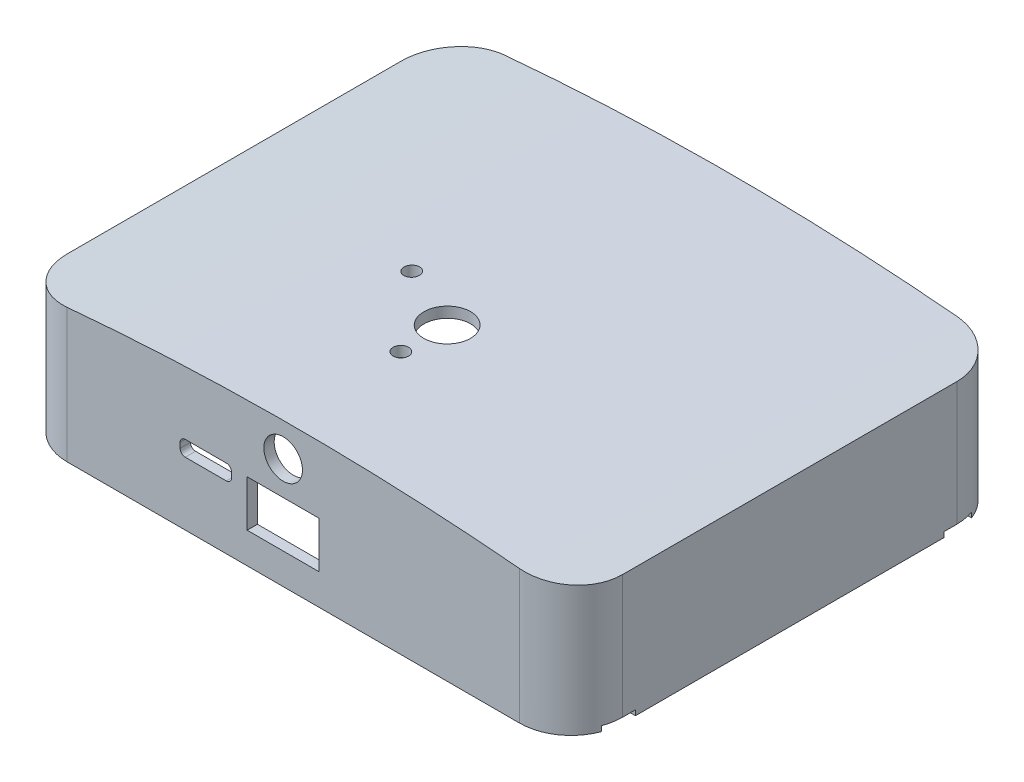
SolidWorks part; units mm, degrees
ref_plane "Front Plane" through (0, 0, 0) normal (0, 0, 1) x (1, 0, 0)
ref_plane "Top Plane" through (0, 0, 0) normal (0, 1, 0) x (1, 0, 0)
ref_plane "Right Plane" through (0, 0, 0) normal (1, 0, 0) x (0, 0, -1)
ref_plane "Plane2" through (0, 0, -85) normal (0, 0, 1) x (1, 0, 0)
ref_plane "Plane3" through (0, 2, 0) normal (0, 1, 0) x (1, 0, 0)
sketch "Sketch10" plane through (0, 2, 0) normal (0, 1, 0) x (1, 0, 0)
  line L0 (57.999, 83) -> (-30.001, 83)
  line L1 (-38.001, 75) -> (-38.001, 10)
  line L2 (-30.001, 2) -> (57.999, 2)
  line L3 (65.999, 10) -> (65.999, 75)
  line L12 (67.999, 10) -> (67.999, 75)
  line L13 (-30.001, 0) -> (57.999, 0)
  line L14 (-40.001, 75) -> (-40.001, 10)
  line L15 (57.999, 85) -> (-30.001, 85)
  arc A0 (65.999, 75) -> (57.999, 83) centre (57.999, 75) ccw
  arc A1 (-30.001, 83) -> (-38.001, 75) centre (-30.001, 75) ccw
  arc A2 (-38.001, 10) -> (-30.001, 2) centre (-30.001, 10) ccw
  arc A3 (57.999, 2) -> (65.999, 10) centre (57.999, 10) ccw
  arc A12 (67.999, 75) -> (57.999, 85) centre (57.999, 75) ccw
  arc A13 (57.999, 0) -> (67.999, 10) centre (57.999, 10) ccw
  arc A14 (-40.001, 10) -> (-30.001, 0) centre (-30.001, 10) ccw
  arc A15 (-30.001, 85) -> (-40.001, 75) centre (-30.001, 75) ccw
  dimension "D1" = 2
extrude "Boss-Extrude5" add sketch "Sketch10" along normal blind 42
sketch "Sketch20" plane through (0, 0, 0) normal (0, 0, 1) x (1, 0, 0)
  line L0 (-40.001, 25) -> (67.999, 25) construction
  line L1 (-32.001, 5) -> (18.999, 5) construction
  line L2 (-32.001, 5) -> (-32.001, 25) construction
  line L3 (-32.001, 25) -> (18.999, 25) construction
  line L4 (18.999, 5) -> (18.999, 25) construction
  line L5 (-40.001, 44) -> (-40.001, 2) construction
  line L6 (67.999, 44) -> (67.999, 2) construction
  line L7 (13.999, 25) -> (13.999, 27.03) construction
  line L9 (13.999, 25) -> (13.999, 28.9912) construction
  line L10 (13.999, 25) -> (13.999, 30.9628) construction
  line L11 (-40.001, 25) -> (-40.001, 27.03)
  line L12 (67.999, 25) -> (67.999, 27.03)
  line L13 (13.999, 25) -> (13.999, 27.9584) construction
  line L14 (13.999, 25) -> (13.999, 30.0146) construction
  spline S1 degree 2 poles (-40.001, 25) (13.999, 30.9168) (67.999, 25) knots 0 0 0 1 1 1
  spline S2 degree 2 poles (67.999, 27.03) (13.999, 32.9992) (-40.001, 27.03) knots 0 0 0 1 1 1
  dimension "D1" = 20
sketch "Sketch22" plane through (0, 0, 0) normal (0, 0, 1) x (1, 0, 0)
  line L0 (67.999, 44) -> (67.999, 2) construction
  line L1 (67.999, 44) -> (57.999, 44) construction
  line L2 (-30.001, 44) -> (-40.001, 44) construction
  line L3 (-30.001, 44) -> (57.999, 44) construction
  line L4 (-40.001, 44) -> (-40.001, 2) construction
  line L5 (67.999, 44) -> (67.999, 25)
  line L6 (67.999, 44) -> (57.999, 44)
  line L7 (-30.001, 44) -> (-40.001, 44)
  line L8 (-30.001, 44) -> (57.999, 44)
  line L9 (-40.001, 44) -> (-40.001, 25)
  line L10 (-40.001, 25) -> (67.999, 25) construction
  line L11 (13.999, 25) -> (13.999, 28.0496) construction
  spline S0 degree 2 poles (-40.001, 25) (13.999, 31.0992) (67.999, 25) knots 0 0 0 1 1 1
extrude "Cut-Extrude6" cut sketch "Sketch22" against normal blind 95
extrude "Boss-Extrude8" add sketch "Sketch20" against normal blind 85
sketch "Sketch23" plane through (0, 2, 0) normal (0, -1, 0) x (1, 0, 0)
  line L0 (-40.001, -75) -> (-40.001, -85) construction
  line L1 (-40.001, -85) -> (-30.001, -85) construction
  line L2 (57.999, -85) -> (67.999, -85) construction
  line L3 (67.999, -85) -> (67.999, -75) construction
  line L4 (67.999, -10) -> (67.999, 0) construction
  line L5 (67.999, 0) -> (57.999, 0) construction
  line L6 (-30.001, 0) -> (-40.001, 0) construction
  line L7 (-40.001, 0) -> (-40.001, -10) construction
  line L8 (-40.001, -75) -> (-40.001, -85)
  line L9 (-40.001, -85) -> (-30.001, -85)
  line L10 (57.999, -85) -> (67.999, -85)
  line L11 (67.999, -85) -> (67.999, -75)
  line L12 (67.999, -10) -> (67.999, 0)
  line L13 (67.999, 0) -> (57.999, 0)
  line L14 (-30.001, 0) -> (-40.001, 0)
  line L15 (-40.001, 0) -> (-40.001, -10)
  arc A0 (-40.001, -75) -> (-30.001, -85) centre (-30.001, -75) ccw construction
  arc A1 (57.999, -85) -> (67.999, -75) centre (57.999, -75) ccw construction
  arc A2 (67.999, -10) -> (57.999, 0) centre (57.999, -10) ccw construction
  arc A3 (-30.001, 0) -> (-40.001, -10) centre (-30.001, -10) ccw construction
  arc A4 (-40.001, -75) -> (-30.001, -85) centre (-30.001, -75) ccw
  arc A5 (57.999, -85) -> (67.999, -75) centre (57.999, -75) ccw
  arc A6 (67.999, -10) -> (57.999, 0) centre (57.999, -10) ccw
  arc A7 (-30.001, 0) -> (-40.001, -10) centre (-30.001, -10) ccw
extrude "Cut-Extrude7" cut sketch "Sketch23" against normal blind 85
sketch "Sketch26" plane through (0, 0, 0) normal (0, 0, 1) x (1, 0, 0)
  line L0 (-32.001, 5) -> (18.999, 5) construction
  line L1 (-40.001, 14.515) -> (67.999, 14.515) construction
  line L2 (-40.001, 27.03) -> (-40.001, 2) construction
  line L3 (67.999, 27.03) -> (67.999, 2) construction
  line L4 (13.999, 14.515) -> (13.999, 36.3942) construction
  line L5 (18.999, 5) -> (18.999, 26.3407) construction
  line L6 (4.999, 17) -> (18.999, 17)
  line L7 (4.999, 17) -> (4.999, 8)
  line L8 (4.999, 8) -> (18.999, 8)
  line L9 (18.999, 17) -> (18.999, 8)
  line L10 (11.999, 17) -> (11.999, 30.0105) construction
  circle A0 centre (11.999, 23.5) radius 3.75
  parabola Q0 (57.999, 28.033) -> (-30.001, 28.033) focus (13.999, -214.2381) apex (13.999, 30.0146) construction
  dimension "D6" = 7.5
  dimension "D1" = 14
  dimension "D2" = 9
  dimension "D3" = 0
  dimension "D4" = 3
  dimension "D5" = 6.5
extrude "Cut-Extrude9" cut sketch "Sketch26" against normal blind 15 contours L9 L6 L7 L8 | A0
sketch "Sketch28" plane through (0, 2, 0) normal (0, -1, 0) x (1, 0, 0)
  line L4 (-30.001, -85) -> (57.999, -85)
  line L5 (67.999, -75) -> (67.999, -10)
  line L6 (57.999, 0) -> (-30.001, 0)
  line L7 (-40.001, -10) -> (-40.001, -75)
  line L9 (67.999, -75) -> (67.999, -72.5)
  line L11 (-40.001, -10) -> (-40.001, -12.5)
  line L18 (63.999, -12.5) -> (67.999, -12.5)
  line L19 (67.3665, -6.5) -> (63.999, -6.5)
  line L20 (63.999, -78.5) -> (67.3665, -78.5)
  line L21 (-40.001, -72.5) -> (-40.001, -75)
  line L22 (67.999, -72.5) -> (63.999, -72.5)
  line L23 (-39.3685, -78.5) -> (-36.001, -78.5)
  line L24 (-36.001, -72.5) -> (-40.001, -72.5)
  line L26 (-40.001, -12.5) -> (-36.001, -12.5)
  line L27 (-36.001, -6.5) -> (-39.3685, -6.5)
  line L28 (67.999, -12.5) -> (67.999, -10)
  arc A4 (57.999, -85) -> (67.999, -75) centre (57.999, -75) ccw
  arc A5 (67.999, -10) -> (57.999, 0) centre (57.999, -10) ccw
  arc A6 (-30.001, 0) -> (-40.001, -10) centre (-30.001, -10) ccw
  arc A7 (-40.001, -75) -> (-30.001, -85) centre (-30.001, -75) ccw
  arc A8 (67.3665, -78.5) -> (67.999, -75) centre (57.999, -75) ccw
  arc A9 (67.999, -10) -> (67.3665, -6.5) centre (57.999, -10) ccw
  arc A10 (-39.3685, -6.5) -> (-40.001, -10) centre (-30.001, -10) ccw
  arc A11 (-40.001, -75) -> (-39.3685, -78.5) centre (-30.001, -75) ccw
  arc A16 (63.999, -6.5) -> (63.999, -12.5) centre (63.999, -9.5) ccw
  arc A19 (63.999, -72.5) -> (63.999, -78.5) centre (63.999, -75.5) ccw
  arc A21 (-36.001, -78.5) -> (-36.001, -72.5) centre (-36.001, -75.5) ccw
  arc A23 (-36.001, -12.5) -> (-36.001, -6.5) centre (-36.001, -9.5) ccw
  dimension "D1" = 0
extrude "Boss-Extrude9" add sketch "Sketch28" against normal blind 15
sketch "Sketch29" plane through (0, 2, 0) normal (0, -1, 0) x (1, 0, 0)
  line L14 (67.999, -72.5) -> (67.999, -75)
  line L15 (63.999, -12.5) -> (67.999, -12.5)
  line L16 (67.3665, -6.5) -> (63.999, -6.5)
  line L17 (-40.001, -12.5) -> (-40.001, -10)
  line L18 (67.999, -10) -> (67.999, -12.5)
  line L19 (67.999, -72.5) -> (63.999, -72.5)
  line L20 (63.999, -78.5) -> (67.3665, -78.5)
  line L22 (-39.3685, -78.5) -> (-36.001, -78.5)
  line L23 (-36.001, -72.5) -> (-40.001, -72.5)
  line L24 (-40.001, -75) -> (-40.001, -72.5)
  line L26 (-40.001, -12.5) -> (-36.001, -12.5)
  line L27 (-36.001, -6.5) -> (-39.3685, -6.5)
  arc A12 (67.999, -10) -> (67.3665, -6.5) centre (57.999, -10) ccw
  arc A14 (63.999, -6.5) -> (63.999, -12.5) centre (63.999, -9.5) ccw
  arc A16 (67.3665, -78.5) -> (67.999, -75) centre (57.999, -75) ccw
  arc A17 (63.999, -72.5) -> (63.999, -78.5) centre (63.999, -75.5) ccw
  arc A18 (-40.001, -75) -> (-39.3685, -78.5) centre (-30.001, -75) ccw
  arc A20 (-36.001, -78.5) -> (-36.001, -72.5) centre (-36.001, -75.5) ccw
  arc A22 (-39.3685, -6.5) -> (-40.001, -10) centre (-30.001, -10) ccw
  arc A23 (-36.001, -12.5) -> (-36.001, -6.5) centre (-36.001, -9.5) ccw
extrude "Cut-Extrude11" cut sketch "Sketch29" against normal blind 1
sketch "Sketch30" plane through (0, 3, 0) normal (0, -1, 0) x (1, 0, 0)
  circle A0 centre (-36.001, -9.5) radius 1.4
  circle A1 centre (63.999, -9.5) radius 1.4
  circle A2 centre (63.999, -75.5) radius 1.4
  circle A3 centre (-36.001, -75.5) radius 1.4
extrude "Cut-Extrude12" cut sketch "Sketch30" against normal blind 15
sketch "Sketch31" plane through (-40.001, 0, 0) normal (-1, 0, 0) x (0, 0, 1)
  line L0 (-58.5, 8.5) -> (-58.5, 20.9923) construction
  line L1 (-72.5, 2) -> (-12.5, 2) construction
  line L3 (-62.5639, 14.4802) -> (-54.6165, 14.4802) construction
  line L4 (-63.5, 8.5) -> (-53.5, 8.5)
  line L5 (-52.5, 14.5) -> (-52.5, 9.5)
  line L6 (-63.5, 15.5) -> (-53.5, 15.5)
  line L7 (-64.5, 14.5) -> (-64.5, 9.5)
  line L8 (-62.5639, 14.4802) -> (-62.5639, 12.6695) construction
  line L9 (-62.5639, 12.6695) -> (-54.6165, 12.6695) construction
  line L10 (-54.6165, 14.4802) -> (-54.6165, 12.6695) construction
  arc A4 (-64.5, 9.5) -> (-63.5, 8.5) centre (-63.5, 9.5) ccw
  arc A5 (-53.5, 8.5) -> (-52.5, 9.5) centre (-53.5, 9.5) ccw
  arc A6 (-52.5, 14.5) -> (-53.5, 15.5) centre (-53.5, 14.5) ccw
  arc A7 (-63.5, 15.5) -> (-64.5, 14.5) centre (-63.5, 14.5) ccw
  dimension "D2" = 6.5
extrude "Cut-Extrude17" cut sketch "Sketch31" against normal blind 3
sketch "Sketch32" plane through (0, 2, 0) normal (0, -1, 0) x (1, 0, 0)
  line L0 (-30.001, -2) -> (57.999, -2) construction
  circle A0 centre (11.8847, -32) radius 4.5284
  dimension "D1" = 30
extrude "Cut-Extrude18" cut sketch "Sketch32" against normal blind 42
sketch "Sketch33" plane through (0, 2, 0) normal (0, -1, 0) x (1, 0, 0)
  line L0 (-30.001, -2) -> (57.999, -2) construction
  circle A0 centre (11.8847, -23) radius 1.5
  dimension "D1" = 3
  dimension "D2" = 21
extrude "Cut-Extrude19" cut sketch "Sketch33" against normal blind 42
sketch "Sketch34" plane through (0, 0, 0) normal (0, 0, 1) x (1, 0, 0)
  line L1 (-7.039, 17.277) -> (0.961, 17.277)
  line L2 (-8.039, 16.277) -> (-8.039, 15.277)
  line L3 (-7.039, 14.277) -> (0.961, 14.277)
  line L4 (1.961, 16.277) -> (1.961, 15.277)
  arc A0 (1.961, 15.277) -> (0.961, 14.277) centre (0.961, 15.277) cw
  arc A1 (1.961, 16.277) -> (0.961, 17.277) centre (0.961, 16.277) ccw
  arc A2 (-7.039, 14.277) -> (-8.039, 15.277) centre (-7.039, 15.277) cw
  arc A3 (-8.039, 16.277) -> (-7.039, 17.277) centre (-7.039, 16.277) cw
  point P8 (1.961, 17.277)
  point P11 (-8.039, 14.277)
  point P14 (-8.039, 17.277)
  dimension "D3" = 1
  dimension "D1" = 10
  dimension "D2" = 3
extrude "Cut-Extrude20" cut sketch "Sketch34" against normal blind 3 contours L4 L1 L2 L3
sketch "Sketch35" plane through (0, 2, 0) normal (0, -1, 0) x (1, 0, 0)
  circle A0 centre (-0.8366, -37.8264) radius 1.5
  dimension "D1" = 3
extrude "Cut-Extrude21" cut sketch "Sketch35" against normal blind 98
sketch "Sketch36" plane through (-40.001, 0, 0) normal (-1, 0, 0) x (0, 0, 1)
  line L0 (-53.5, 15.5) -> (-63.5, 15.5) construction
  line L1 (-64.5, 16.5) -> (-52.5, 16.5)
  line L2 (-66.5, 14.5) -> (-66.5, 9.5)
  line L3 (-64.5, 7.5) -> (-52.5, 7.5)
  line L4 (-50.5, 14.5) -> (-50.5, 9.5)
  line L6 (-66.5, 12) -> (-50.5, 12) construction
  line L7 (-63.5, 8.5) -> (-53.5, 8.5) construction
  line L9 (-58.5, 12) -> (-58.5, 17.9769) construction
  arc A0 (-64.5, 7.5) -> (-66.5, 9.5) centre (-64.5, 9.5) cw
  arc A1 (-50.5, 9.5) -> (-52.5, 7.5) centre (-52.5, 9.5) cw
  arc A2 (-50.5, 14.5) -> (-52.5, 16.5) centre (-52.5, 14.5) ccw
  arc A3 (-64.5, 16.5) -> (-66.5, 14.5) centre (-64.5, 14.5) ccw
  dimension "D5" = 2
  dimension "D1" = 1
  dimension "D2" = 1
  dimension "D3" = 8
  dimension "D4" = 8
extrude "Cut-Extrude22" cut sketch "Sketch36" against normal blind 3
